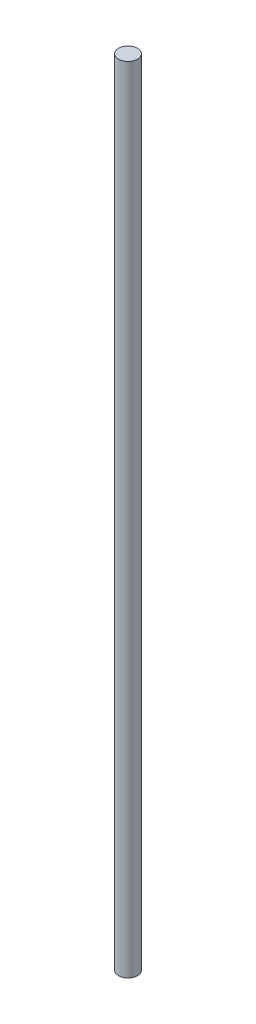
SolidWorks part; units mm, degrees
ref_plane "Front Plane" through (0, 0, 0) normal (0, 0, 1) x (1, 0, 0)
ref_plane "Top Plane" through (0, 0, 0) normal (0, 1, 0) x (1, 0, 0)
ref_plane "Right Plane" through (0, 0, 0) normal (1, 0, 0) x (0, 0, -1)
sketch "Sketch1" plane through (0, 0, 0) normal (0, 0, 1) x (1, 0, 0)
  line L0 (4, 167.5) -> (0, 167.5)
  line L1 (0, 167.5) -> (0, -167.5)
  line L2 (0, -167.5) -> (4, -167.5)
  line L3 (4, -167.5) -> (4, 167.5)
  line L4 (0, 167.5) -> (0, -167.5) construction
revolve "Revolve1" add sketch "Sketch1" angle 360 about L4
